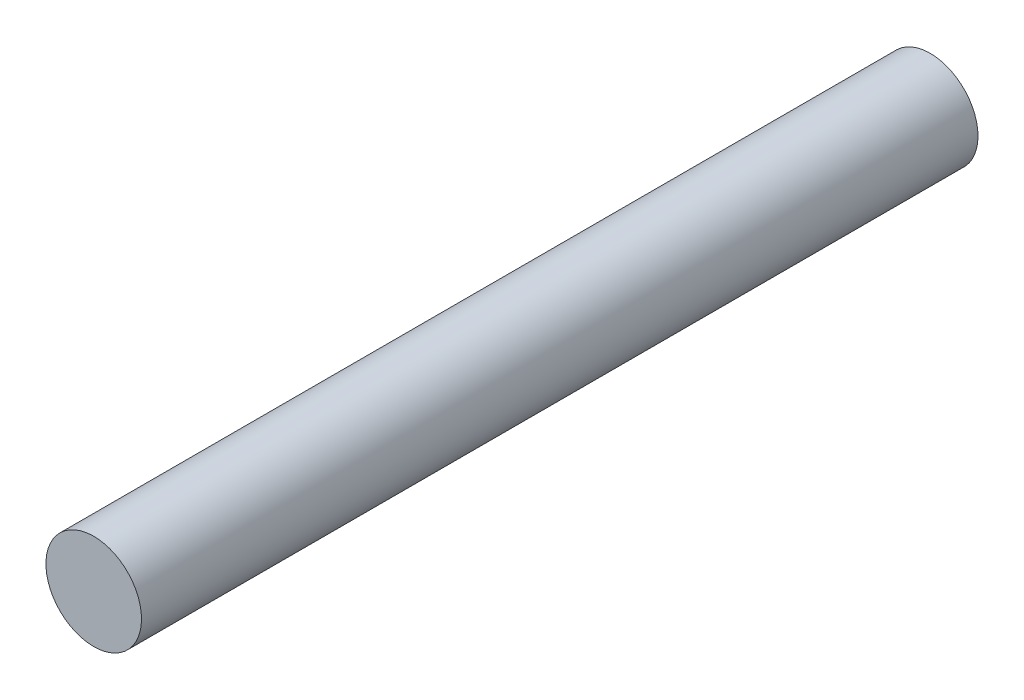
SolidWorks part; units mm, degrees
ref_plane "前视基准面" through (0, 0, 0) normal (0, 0, 1) x (1, 0, 0)
ref_plane "上视基准面" through (0, 0, 0) normal (0, 1, 0) x (1, 0, 0)
ref_plane "右视基准面" through (0, 0, 0) normal (1, 0, 0) x (0, 0, -1)
sketch "草图1" plane through (0, 0, 0) normal (0, 0, 1) x (1, 0, 0)
  circle A0 centre (0, 0) radius 4
  dimension "D1" = 8
extrude "凸台-拉伸1" add sketch "草图1" along normal blind 70
